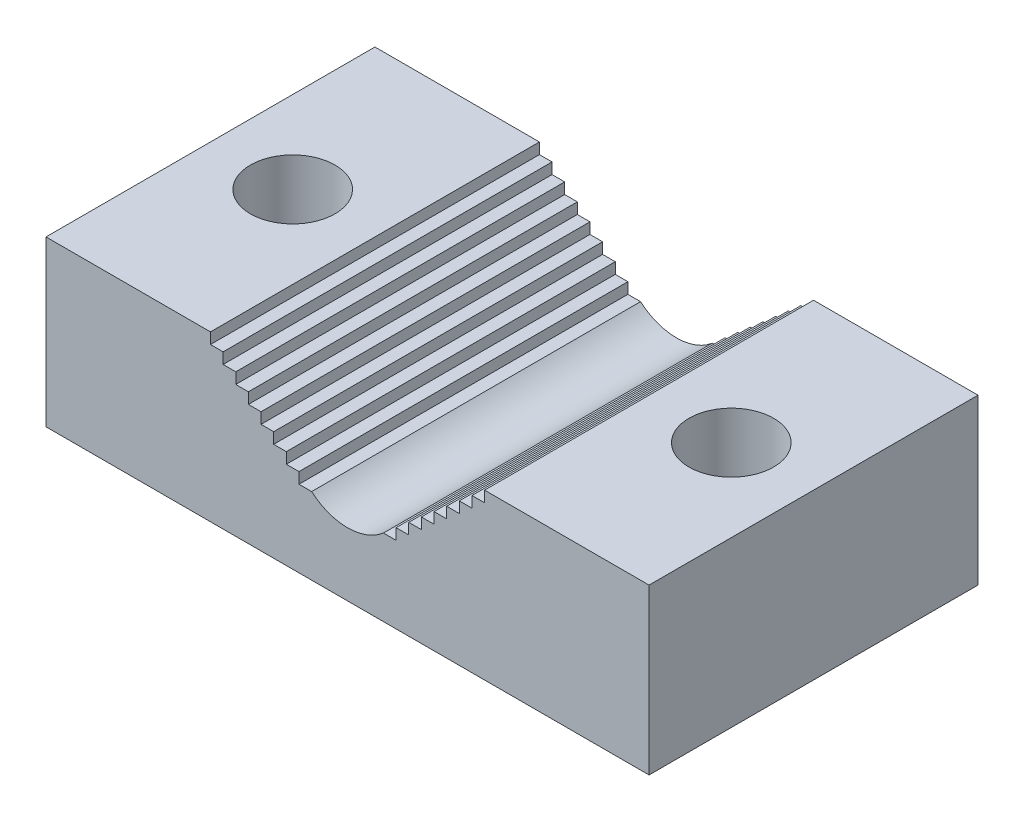
SolidWorks part; units mm, degrees
material "6061-T6 (SS)"
ref_plane "Front Plane" through (0, 0, 0) normal (0, 0, 1) x (1, 0, 0)
ref_plane "Top Plane" through (0, 0, 0) normal (0, 1, 0) x (1, 0, 0)
ref_plane "Right Plane" through (0, 0, 0) normal (1, 0, 0) x (0, 0, -1)
sketch "Sketch1" plane through (0, 0, 0) normal (0, 0, 1) x (1, 0, 0)
  line L0 (-34.925, 0) -> (34.925, 0)
  line L1 (34.925, 0) -> (34.925, 19.05)
  line L2 (34.925, 19.05) -> (-34.925, 19.05)
  line L3 (-34.925, 19.05) -> (-34.925, 0)
  point P3 (0, 0)
  dimension "D1" = 19.05
  dimension "D2" = 69.85
extrude "Boss-Extrude1" add sketch "Sketch1" against normal blind 38.1
sketch "Sketch2" plane through (0, 0, 0) normal (0, 0, 1) x (1, 0, 0)
  line L0 (-15.875, 19.05) -> (-4.1606, 8.89) construction
  line L1 (-15.875, 19.05) -> (0, 19.05)
  line L2 (34.925, 19.05) -> (-34.925, 19.05) construction
  line L3 (15.875, 19.05) -> (4.1606, 8.89) construction
  line L4 (15.875, 19.05) -> (0, 19.05)
  line L5 (-15.875, 19.05) -> (-15.875, 17.78)
  line L6 (-15.875, 17.78) -> (-14.4107, 17.78)
  line L7 (-14.4107, 17.78) -> (-14.4107, 16.51)
  line L8 (-14.4107, 16.51) -> (-12.9464, 16.51)
  line L9 (-12.9464, 16.51) -> (-12.9464, 15.24)
  line L10 (-12.9464, 15.24) -> (-11.4821, 15.24)
  line L11 (-11.4821, 15.24) -> (-11.4821, 13.97)
  line L12 (-11.4821, 13.97) -> (-10.0178, 13.97)
  line L13 (-10.0178, 13.97) -> (-10.0178, 12.7)
  line L14 (-10.0178, 12.7) -> (-8.5535, 12.7)
  line L15 (-8.5535, 12.7) -> (-8.5535, 11.43)
  line L16 (-8.5535, 11.43) -> (-7.0892, 11.43)
  line L17 (-7.0892, 11.43) -> (-7.0892, 10.16)
  line L18 (-7.0892, 10.16) -> (-5.6249, 10.16)
  line L19 (-5.6249, 10.16) -> (-5.6249, 8.89)
  line L20 (-5.6249, 8.89) -> (-4.1606, 8.89)
  line L21 (0, 19.05) -> (0, 0) construction
  line L24 (5.6249, 8.89) -> (4.1606, 8.89)
  line L25 (5.6249, 10.16) -> (5.6249, 8.89)
  line L26 (7.0892, 10.16) -> (5.6249, 10.16)
  line L27 (7.0892, 11.43) -> (7.0892, 10.16)
  line L28 (8.5535, 11.43) -> (7.0892, 11.43)
  line L29 (8.5535, 12.7) -> (8.5535, 11.43)
  line L30 (10.0178, 12.7) -> (8.5535, 12.7)
  line L31 (10.0178, 13.97) -> (10.0178, 12.7)
  line L32 (11.4821, 13.97) -> (10.0178, 13.97)
  line L33 (11.4821, 15.24) -> (11.4821, 13.97)
  line L34 (12.9464, 15.24) -> (11.4821, 15.24)
  line L35 (12.9464, 16.51) -> (12.9464, 15.24)
  line L36 (14.4107, 16.51) -> (12.9464, 16.51)
  line L37 (14.4107, 17.78) -> (14.4107, 16.51)
  line L38 (15.875, 17.78) -> (14.4107, 17.78)
  line L39 (15.875, 19.05) -> (15.875, 17.78)
  arc A0 (4.1606, 8.89) -> (-4.1606, 8.89) centre (0, 13.6871) cw
  point P7 (0, 19.05)
  dimension "D1" = 6.35
  dimension "D2" = 31.75
  dimension "D4" = 1.27
extrude "Cut-Extrude1" cut sketch "Sketch2" against normal up to next
sketch "Sketch3" plane through (0, 0, 0) normal (0, 0, 1) x (1, 0, 0)
  circle A0 centre (0, 24.151) radius 14.2875
  dimension "D1" = 28.575
hole_wizard "3/8 Clearance Hole1" positions "Sketch6" profile "Sketch5" hole size "3/8" standard "ANSI Inch" end condition through all
sketch "Sketch6" plane through (0, 19.05, 0) normal (0, 1, 0) x (1, 0, 0)
  line L0 (-15.875, 38.1) -> (-34.925, 38.1) construction
  line L1 (-34.925, 38.1) -> (-34.925, 0) construction
  line L2 (34.925, 38.1) -> (15.875, 38.1) construction
  line L3 (34.925, 38.1) -> (34.925, 0) construction
  point P0 (-25.4, 19.05)
  point P2 (25.4, 19.05)
  point P7 (-25.4, 38.1)
  point P10 (-34.925, 19.05)
  point P13 (25.4, 38.1)
  point P16 (34.925, 19.05)
sketch "Sketch5" plane through (-25.4, 19.05, -19.05) normal (1, 0, 0) x (0, 0, 1)
  line L0 (0, 0) -> (0, 19.05)
  line L1 (0, 19.05) -> (4.9022, 19.05)
  line L2 (4.9022, 19.05) -> (4.9022, 0)
  line L5 (4.9022, 0) -> (0, 0)
  line L11 (0, -6.35) -> (0, 107.95) construction
  dimension "Thru Hole Dia." = 9.8044
  dimension "Thru Hole Depth" = 19.05
